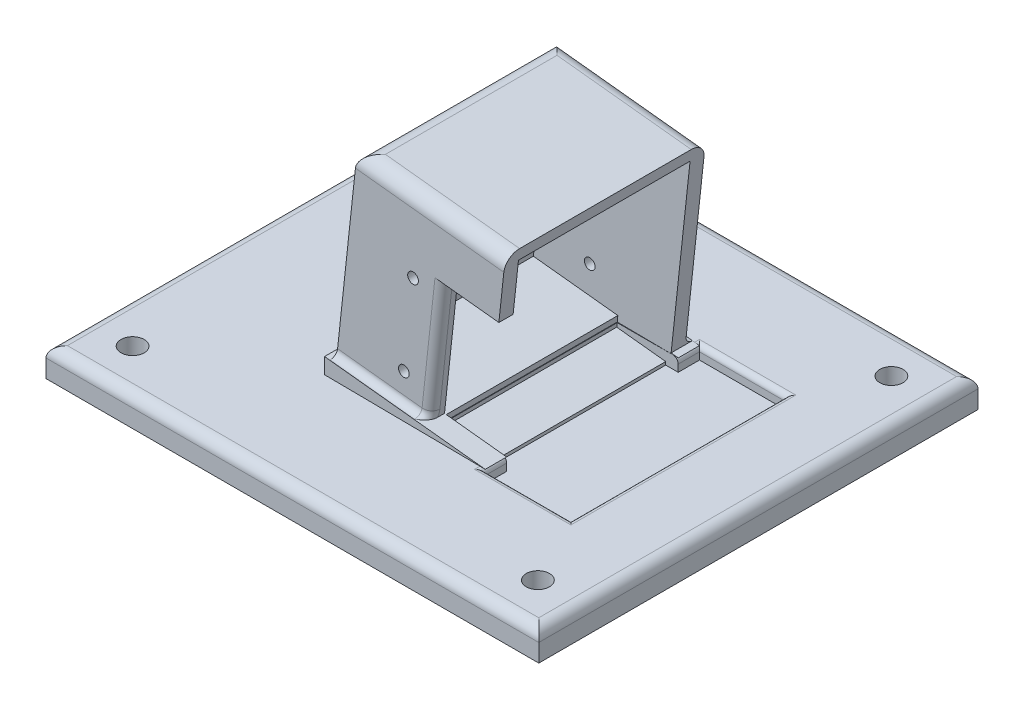
SolidWorks part; units mm, degrees
ref_plane "Front Plane" through (0, 0, 0) normal (0, 0, 1) x (1, 0, 0)
ref_plane "Top Plane" through (0, 0, 0) normal (0, 1, 0) x (1, 0, 0)
ref_plane "Right Plane" through (0, 0, 0) normal (1, 0, 0) x (0, 0, -1)
sketch "Sketch1" plane through (0, 0, 0) normal (0, 0, 1) x (1, 0, 0)
  line L0 (-31.8084, 0) -> (106.1916, 0)
  line L1 (106.1916, 0) -> (106.1916, 8)
  line L2 (106.1916, 8) -> (-31.8084, 8)
  line L3 (-31.8084, 8) -> (-31.8084, 0)
  dimension "D1" = 8
  dimension "D2" = 138
extrude "Boss-Extrude1" add sketch "Sketch1" against normal blind 123
sketch "Sketch2" plane through (0, 8, 0) normal (0, 1, 0) x (1, 0, 0)
  line L0 (-31.8084, 123) -> (-31.8084, 0) construction
  line L1 (106.1916, 123) -> (106.1916, 0) construction
  line L2 (106.1916, 0) -> (-31.8084, 0) construction
  line L3 (106.1916, 123) -> (-31.8084, 123) construction
  circle A0 centre (-19.5584, 12) radius 3.25
  circle A1 centre (93.9416, 12) radius 3.25
  circle A2 centre (93.9416, 111) radius 3.25
  circle A3 centre (-19.5584, 111) radius 3.25
  dimension "D1" = 6.5
  dimension "D2" = 6.5
  dimension "D3" = 6.5
  dimension "D4" = 6.5
  dimension "D5" = 12.25
  dimension "D6" = 12.25
  dimension "D7" = 12
  dimension "D8" = 12
  dimension "D9" = 12.25
  dimension "D10" = 12
  dimension "D11" = 12.25
  dimension "D12" = 12
extrude "Cut-Extrude1" cut sketch "Sketch2" against normal through all
ref_plane "Plane1" through (0, 0, -31.5) normal (0, 0, 1) x (1, 0, 0)
sketch "Sketch3" plane through (0, 0, -31.5) normal (0, 0, 1) x (1, 0, 0)
  line L0 (14.6916, 8.4364) -> (59.6916, 8)
  line L1 (106.1916, 8) -> (-31.8084, 8) construction
  line L2 (59.6916, 8) -> (14.6916, 12.8564)
  line L3 (14.6916, 12.8564) -> (14.6916, 8.4364)
  line L5 (106.1916, 0) -> (106.1916, 8) construction
  dimension "D1" = 45
  dimension "D2" = 46.5
  dimension "D3" = 4.42
  dimension "D4" = 5.604
extrude "Boss-Extrude2" add sketch "Sketch3" against normal blind 60 separate body
sketch "Sketch5" plane through (1.5406, 14.2757, 0) normal (0.1073, 0.9942, 0) x (0.9942, -0.1073, 0)
  line L0 (56.4886, 33.5) -> (14.6886, 33.5)
  line L1 (14.6886, 33.5) -> (14.6886, 89.55)
  line L2 (14.6886, 89.55) -> (56.4886, 89.55)
  line L3 (56.4886, 89.55) -> (56.4886, 85.55)
  line L4 (56.4886, 85.55) -> (17.6886, 85.55)
  line L5 (17.6886, 85.55) -> (17.6886, 37.5)
  line L6 (17.6886, 37.5) -> (56.4886, 37.5)
  line L7 (56.4886, 37.5) -> (56.4886, 33.5)
  line L8 (-2.75, 31.5) -> (2.75, 31.5) construction
  line L9 (58.4886, 91.5) -> (58.4886, 31.5) construction
  point P10 (56.4886, 87.55)
  dimension "D1" = 4
  dimension "D2" = 4
  dimension "D3" = 3
  dimension "D4" = 2
  dimension "D5" = 48.05
  dimension "D6" = 38.8
  dimension "D7" = 2
  dimension "D8" = 2
extrude "Boss-Extrude3" add sketch "Sketch5" along normal blind 49.45
sketch "Sketch6" plane through (0, 0, -33.5) normal (0, 0, 1) x (1, 0, 0)
  line L0 (21.4503, 61.8641) -> (16.1445, 12.6996) construction
  line L1 (59.6916, 8) -> (14.6916, 12.8564) construction
  circle A0 centre (34.9065, 18.4195) radius 1.5
  circle A1 centre (37.4816, 42.281) radius 1.5
  dimension "D1" = 3
  dimension "D2" = 3
  dimension "D3" = 18.04
  dimension "D4" = 18.04
  dimension "D5" = 24
  dimension "D6" = 7.7
extrude "Cut-Extrude2" cut sketch "Sketch6" against normal through all
sketch "Sketch8" plane through (0, 0, -37.5) normal (0, 0, -1) x (-1, 0, 0)
  line L0 (-57.7032, 8.2146) -> (-42.2926, 9.8777)
  line L1 (-57.7032, 8.2146) -> (-19.1272, 12.3777) construction
  line L2 (-42.2926, 9.8777) -> (-46.1017, 45.1728)
  line L3 (-46.1017, 45.1728) -> (-61.5122, 43.5097)
  line L4 (-63.009, 57.3791) -> (-57.7032, 8.2146) construction
  line L5 (-61.5122, 43.5097) -> (-57.7032, 8.2146)
  dimension "D1" = 15.5
  dimension "D2" = 35.5
extrude "Cut-Extrude3" cut sketch "Sketch8" against normal blind 4
sketch "Sketch9" plane through (14.6038, -1.576, 0) normal (-0.9942, 0.1073, 0) x (0, 0, 1)
  line L0 (-89.55, 63.8086) -> (-89.55, 14.3586) construction
  line L1 (-89.55, 14.3586) -> (-33.5, 14.3586) construction
  circle A0 centre (-60.55, 34.3586) radius 15.125
  dimension "D1" = 30.25
  dimension "D2" = 29
  dimension "D3" = 20
extrude "Cut-Extrude4" cut sketch "Sketch9" against normal blind 3
sketch "Sketch10" plane through (1.5406, 14.2757, 0) normal (0.1073, 0.9942, 0) x (0.9942, -0.1073, 0)
  line L0 (56.4886, 85.55) -> (41.4886, 85.55)
  line L1 (17.6886, 85.55) -> (56.4886, 85.55) construction
  line L2 (41.4886, 85.55) -> (41.4886, 37.5)
  line L3 (41.4886, 37.5) -> (56.4886, 37.5)
  line L4 (56.4886, 37.5) -> (56.4886, 85.55)
  line L5 (17.6886, 37.5) -> (17.6886, 85.55) construction
  point P6 (48.9886, 85.55)
  point P7 (48.9886, 37.5)
  dimension "D1" = 23.8
  dimension "D2" = 15
  dimension "D3" = 48.05
extrude "Cut-Extrude5" cut sketch "Sketch10" against normal blind 3
sketch "Sketch11" plane through (14.6038, -1.576, 0) normal (-0.9942, 0.1073, 0) x (0, 0, 1)
  line L0 (-89.55, 63.8086) -> (-89.55, 66.8086)
  line L1 (-89.55, 66.8086) -> (-33.5, 66.8086)
  line L2 (-33.5, 66.8086) -> (-33.5, 63.8086)
  line L3 (-33.5, 63.8086) -> (-89.55, 63.8086)
  dimension "D1" = 3
extrude "Boss-Extrude4" add sketch "Sketch11" against normal blind 41.8
sketch "Sketch12" plane through (0, 8, 0) normal (0, 1, 0) x (1, 0, 0)
  line L0 (59.6916, 91.5) -> (83.6816, 91.5)
  line L1 (83.6816, 91.5) -> (83.6816, 31.5)
  line L2 (83.6816, 31.5) -> (59.6916, 31.5)
  line L3 (59.6916, 91.5) -> (59.6916, 31.5) construction
  line L4 (59.6916, 31.5) -> (59.6916, 91.5)
  dimension "D1" = 23.99
  dimension "D2" = 60
extrude "Cut-Extrude6" cut sketch "Sketch12" against normal blind 3.5
fillet "Fillet1" radius 4 3 edges at (42.5516, 62.6043, -89.55) (42.5516, 62.6043, -33.5) (21.7722, 64.8468, -61.525)
fillet "Fillet3" radius 3 4 edges at (37.1916, 8, -123) (37.1916, 8, 0) (-31.8084, 8, -61.5) (106.1916, 8, -61.5)
fillet "Fillet5" radius 1.9 1 edges at (29.2186, 11.2887, -33.5)
fillet "Fillet6" radius 1.9 1 edges at (36.9238, 10.4571, -89.55)
fillet "Fillet7" radius 2.5 2 edges at (44.2991, 28.4697, -33.5) (42.3524, 10.431, -32.9435)
sketch "Sketch13" plane through (1.5406, 14.2757, 0) normal (0.1073, 0.9942, 0) x (0.9942, -0.1073, 0)
  line L0 (56.4886, 37.5) -> (56.4886, 85.55)
  line L1 (56.4886, 85.55) -> (58.4886, 85.55)
  line L2 (58.4886, 91.5) -> (58.4886, 31.5) construction
  line L3 (58.4886, 85.55) -> (58.4886, 37.5)
  line L4 (58.4886, 37.5) -> (56.4886, 37.5)
extrude "Cut-Extrude7" cut sketch "Sketch13" against normal blind 3.5
sketch "Sketch14" plane through (59.6916, 0, 0) normal (1, 0, 0) x (0, 0, -1)
  line L0 (37.5, 8) -> (85.55, 8)
  line L1 (85.55, 8) -> (85.55, 4.5)
  line L2 (91.5, 4.5) -> (31.5, 4.5) construction
  line L3 (85.55, 4.5) -> (37.5, 4.5)
  line L4 (37.5, 4.5) -> (37.5, 8)
extrude "Cut-Extrude8" cut sketch "Sketch14" against normal blind 3.5
fillet "Fillet8" radius 1.5 5 edges at (59.6916, 8, -88.525) (71.6866, 8, -31.5) (83.6816, 8, -61.5) (71.6866, 8, -91.5) (59.6916, 8, -34.5)
